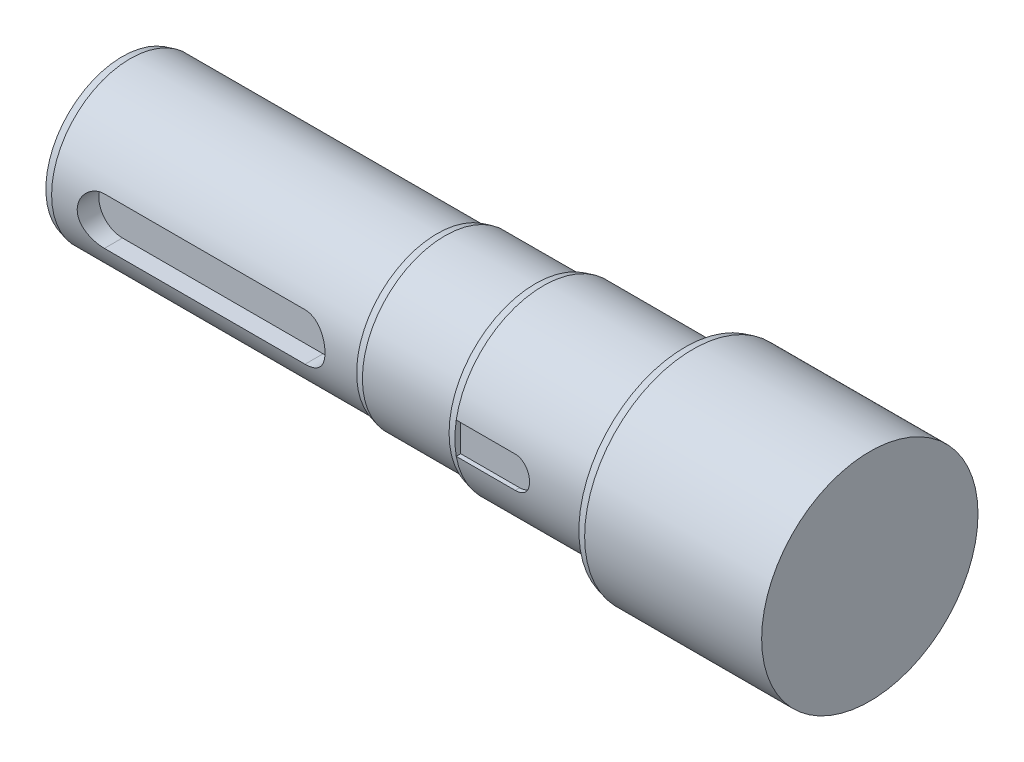
SolidWorks part; units mm, degrees
ref_plane "Ebene vorne" through (0, 0, 0) normal (0, 0, 1) x (1, 0, 0)
ref_plane "Ebene oben" through (0, 0, 0) normal (0, 1, 0) x (1, 0, 0)
ref_plane "Ebene rechts" through (0, 0, 0) normal (1, 0, 0) x (0, 0, -1)
sketch "Skizze1" plane through (0, 0, 0) normal (0, 0, 1) x (1, 0, 0)
  line L0 (-55.0769, 0) -> (85.8247, 0) construction
  line L1 (-85, 22.5) -> (-70, 22.5)
  line L2 (0, 0) -> (0, 27.5)
  line L3 (0, 27.5) -> (-47, 27.5)
  line L6 (-47, 27.5) -> (-47, 22.5)
  line L7 (-70, 22.5) -> (-47, 22.5)
  line L8 (-110, 20) -> (-110, 21)
  line L9 (-110, 21) -> (-85, 21)
  line L10 (-110, 20) -> (-190, 20)
  line L11 (-190, 20) -> (-190, 0)
  line L12 (-190, 0) -> (0, 0)
  line L13 (-85, 21) -> (-85, 22.5)
  point P3 (-150, 20)
  dimension "D1" = 23
  dimension "D2" = 40
  dimension "D3" = 42
  dimension "D8" = 80
  dimension "D9" = 25
  dimension "D10" = 15
revolve "Rotation1" add sketch "Skizze1" angle 360 about L0
chamfer "Fase1" distance 2 angle 15 3 edges at (-47, 0, 27.5) (-85, 0, 22.5) (-110, 0, 21)
ref_plane "Ebene1" through (0, 0, 20) normal (0, 0, 1) x (1, 0, 0)
sketch "Skizze2" plane through (0, 0, 20) normal (0, 0, 1) x (1, 0, 0)
  line L0 (-110, 0) -> (-190, 0) construction
  line L1 (-190, 20) -> (-190, -20) construction
  line L2 (-175.5, 6) -> (-124.5, 6)
  line L4 (-124.5, -6) -> (-175.5, -6)
  arc A0 (-175.5, -6) -> (-175.5, 6) centre (-175.5, 0) cw
  arc A1 (-124.5, 6) -> (-124.5, -6) centre (-124.5, 0) cw
  dimension "D1" = 6
  dimension "D4" = 6
  dimension "D5" = 51
  dimension "D6" = 14.5
  dimension "D2" = 12
  dimension "D3" = 6
extrude "Schnitt-Linear austragen1" cut sketch "Skizze2" against normal blind 5.5
ref_plane "Ebene2" through (0, 0, 22.5) normal (0, 0, 1) x (1, 0, 0)
sketch "Skizze3" plane through (-190, 0, 0) normal (-1, 0, 0) x (0, 0, 1)
  line L0 (0, 36.2616) -> (0, -42.0689) construction
  point P3 (0, 10)
  point P4 (0, -10)
  dimension "D1" = 10
  dimension "D2" = 10
hole_wizard "M8 Gewindebohrung1" positions "Skizze7" profile "Skizze6" tap size "M8" standard "DIN"
sketch "Skizze7" plane through (-190, 0, 0) normal (-1, 0, 0) x (0, 0, 1)
  point P0 (0, 10)
  point P3 (0, -10)
sketch "Skizze6" plane through (-190, 10, 0) normal (0, 1, 0) x (0, 0, 1)
  line L0 (0, 0) -> (0, 22.0429)
  line L1 (0, 22.0429) -> (3.4, 20)
  line L2 (3.4, 20) -> (3.4, 0)
  line L5 (3.4, 0) -> (0, 0)
  line L10 (0, 22.0429) -> (-3.4, 20) construction
  line L11 (0, -6.35) -> (0, 107.95) construction
  dimension "Bohrerdurchmesser" = 6.8
  dimension "Bohrungstiefe" = 20
  dimension "Spitzenwinkel" = 118
cosmetic thread "Bohrungsgewinde3"
cosmetic thread "Bohrungsgewinde4"
chamfer "Fase2" distance 2 angle 15 1 edges at (-190, 0, 20)
sketch "Skizze8" plane through (0, 0, 22.5) normal (0, 0, 1) x (1, 0, 0)
  line L1 (-83, 22.5) -> (-83, -22.5) construction
  line L2 (-83, 4) -> (-68, 4)
  line L4 (-47, 0) -> (-83, 0) construction
  line L5 (-68, -4) -> (-83, -4)
  line L6 (-83, 4) -> (-83, -4)
  arc A0 (-68, -4) -> (-68, 4) centre (-68, 0) ccw
  dimension "D1" = 8
  dimension "D2" = 15
extrude "Schnitt-Linear austragen2" cut sketch "Skizze8" against normal blind 1.5
